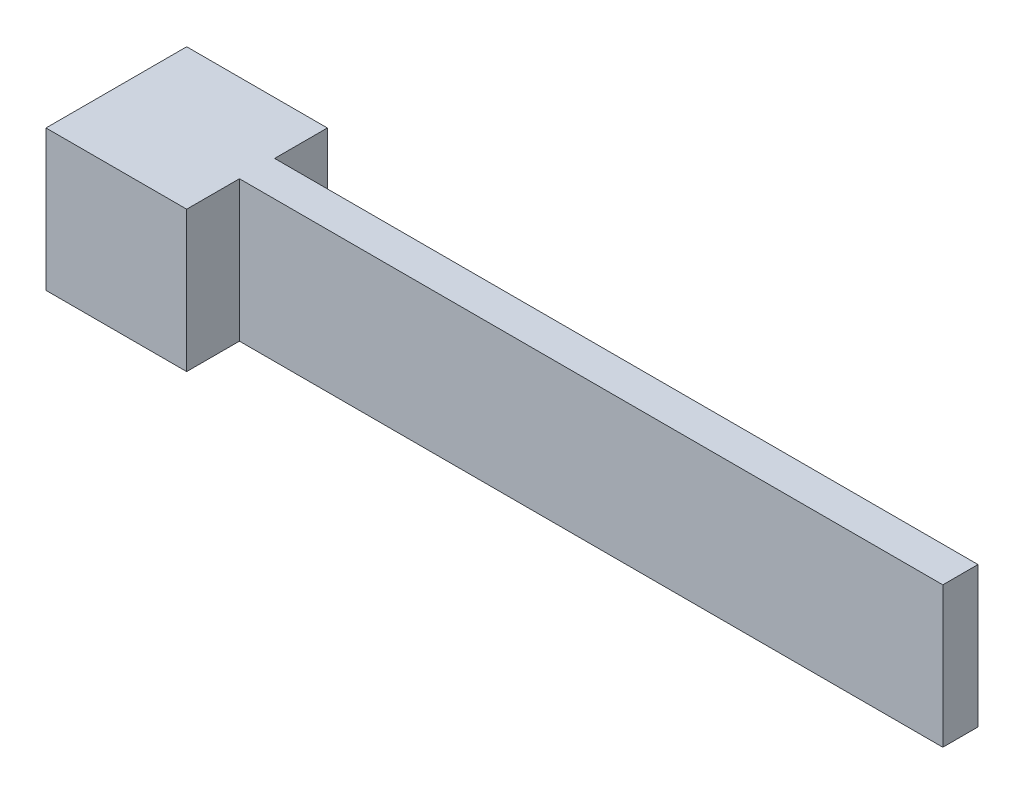
SolidWorks part; units mm, degrees
ref_plane "Front Plane" through (0, 0, 0) normal (0, 0, 1) x (1, 0, 0)
ref_plane "Top Plane" through (0, 0, 0) normal (0, 1, 0) x (1, 0, 0)
ref_plane "Right Plane" through (0, 0, 0) normal (1, 0, 0) x (0, 0, -1)
sketch "Sketch1" plane through (0, 0, 0) normal (1, 0, 0) x (0, 0, -1)
  line L1 (-3, -3) -> (3, -3)
  line L2 (-3, -3) -> (-3, 3)
  line L3 (-3, 3) -> (3, 3)
  line L4 (3, -3) -> (3, 3)
  line L5 (-3, -3) -> (3, 3) construction
  line L6 (-3, 3) -> (3, -3) construction
  point P0 (0, 0)
  dimension "D1" = 6
extrude "Boss-Extrude1" add sketch "Sketch1" along normal blind 6
sketch "Sketch2" plane through (6, 0, 0) normal (1, 0, 0) x (0, 0, -1)
  line L0 (3, 3) -> (-3, 3) construction
  line L1 (-0.75, -3) -> (0.75, -3)
  line L2 (-0.75, -3) -> (-0.75, 3)
  line L3 (-0.75, 3) -> (0.75, 3)
  line L4 (0.75, -3) -> (0.75, 3)
  line L5 (-0.75, -3) -> (0.75, 3) construction
  line L6 (-0.75, 3) -> (0.75, -3) construction
  point P0 (0, 0)
  dimension "D1" = 1.5
extrude "Boss-Extrude2" add sketch "Sketch2" along normal blind 30
sketch "Sketch3" plane through (0, 0, 0) normal (-1, 0, 0) x (0, 0, 1)
  circle A0 centre (0, 0) radius 1.5
extrude "Cut-Extrude1" cut sketch "Sketch3" against normal blind 5
